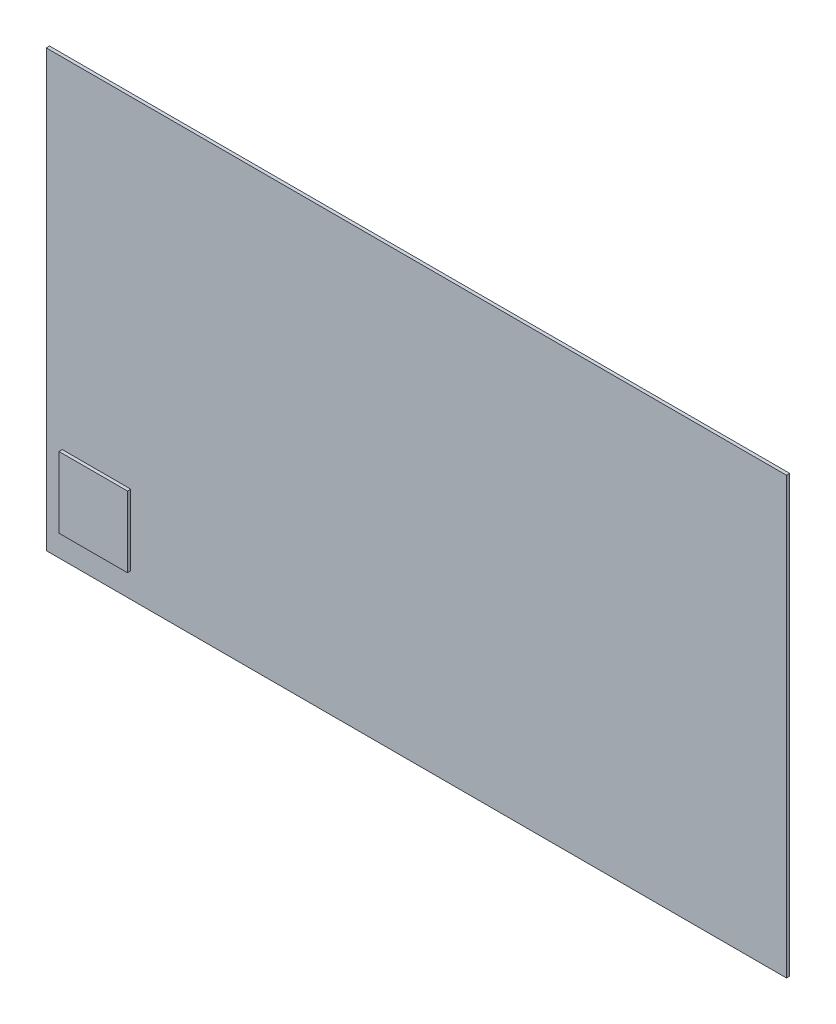
SolidWorks part; units mm, degrees
ref_plane "Front Plane" through (0, 0, 0) normal (0, 0, 1) x (1, 0, 0)
ref_plane "Top Plane" through (0, 0, 0) normal (0, 1, 0) x (1, 0, 0)
ref_plane "Right Plane" through (0, 0, 0) normal (1, 0, 0) x (0, 0, -1)
sketch "Sketch1" plane through (0, 0, 0) normal (0, 0, 1) x (1, 0, 0)
  line L1 (-43.18, 25.4) -> (43.18, 25.4)
  line L2 (-43.18, 25.4) -> (-43.18, -25.4)
  line L3 (-43.18, -25.4) -> (43.18, -25.4)
  line L4 (43.18, 25.4) -> (43.18, -25.4)
  line L5 (-43.18, 25.4) -> (43.18, -25.4) construction
  line L6 (-43.18, -25.4) -> (43.18, 25.4) construction
  point P0 (0, 0)
extrude "Boss-Extrude1" add sketch "Sketch1" along normal blind 0.381
sketch "Sketch2" plane through (0, 0, 0.381) normal (0, 0, 1) x (1, 0, 0)
  line L1 (-41.3182, -14.2548) -> (-33.3246, -14.2548)
  line L2 (-41.3182, -14.2548) -> (-41.3182, -22.5149)
  line L3 (-41.3182, -22.5149) -> (-33.3246, -22.5149)
  line L4 (-33.3246, -14.2548) -> (-33.3246, -22.5149)
  line L5 (-41.3182, -14.2548) -> (-33.3246, -22.5149) construction
  line L6 (-41.3182, -22.5149) -> (-33.3246, -14.2548) construction
  point P0 (-37.3214, -18.3848)
  point P5 (-37.2928, -19.2454)
  point P6 (-37.3231, -19.7511)
  point P7 (-37.3214, -18.3848)
extrude "Boss-Extrude2" add sketch "Sketch2" along normal blind 0.381
